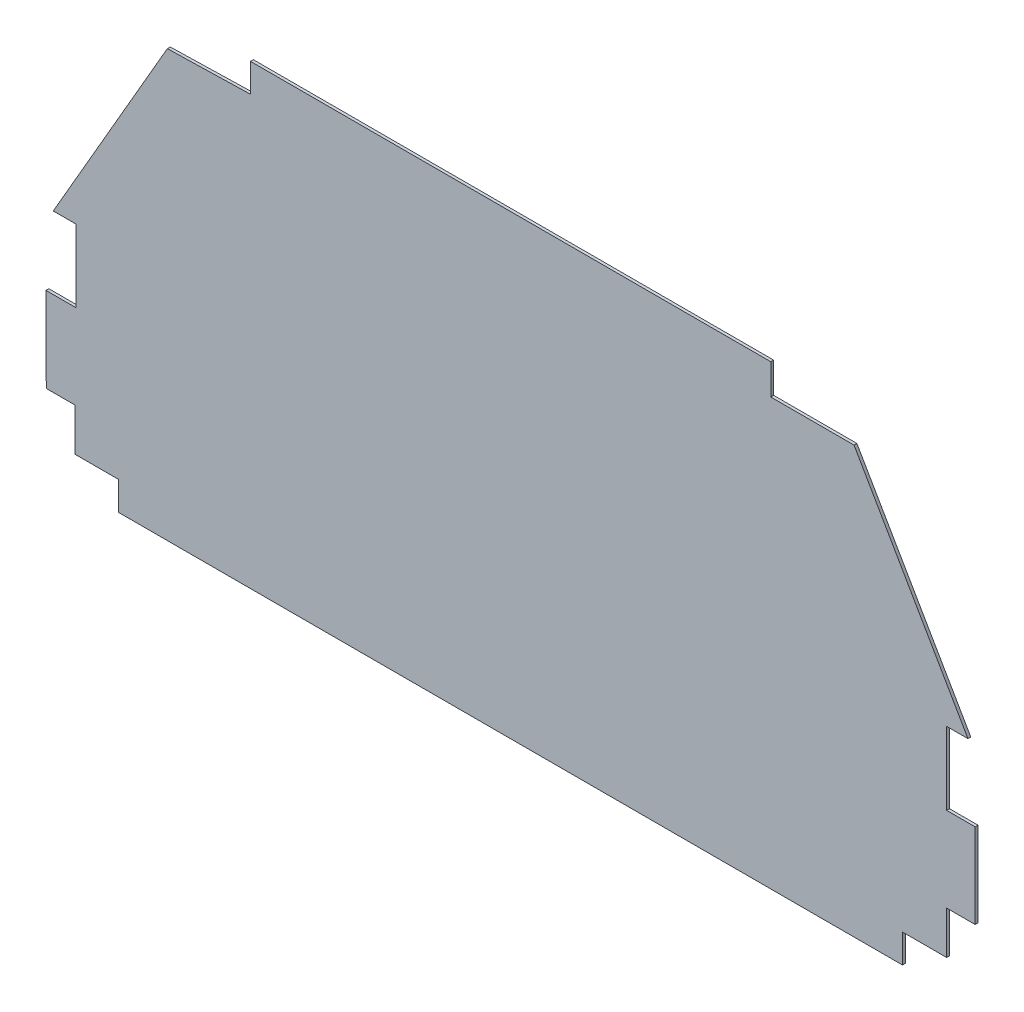
SolidWorks part; units mm, degrees
ref_plane "Front Plane" through (0, 0, 0) normal (0, 0, 1) x (1, 0, 0)
ref_plane "Top Plane" through (0, 0, 0) normal (0, 1, 0) x (1, 0, 0)
ref_plane "Right Plane" through (0, 0, 0) normal (1, 0, 0) x (0, 0, -1)
sketch "Sketch1" plane through (0, 0, 0) normal (0, 0, 1) x (1, 0, 0)
  line L24 (620.5018, 140.3021) -> (635.4651, 140.3021)
  line L25 (620.5018, 89.3201) -> (620.5018, 140.3021)
  line L26 (640.5004, 89.3201) -> (620.5018, 89.3201)
  line L27 (640.5004, 30.0075) -> (640.5004, 89.3201)
  line L28 (620.5018, 30.0075) -> (640.5004, 30.0075)
  line L29 (620.5018, -0.0004) -> (620.5018, 30.0075)
  line L30 (589.5897, -0.0004) -> (620.5018, -0.0004)
  line L31 (589.5897, -20.0284) -> (589.5897, -0.0004)
  line L32 (40.2838, -20.0284) -> (589.5897, -20.0284)
  line L33 (40.2838, -0.0004) -> (40.2838, -20.0284)
  line L34 (9.4987, -0.0004) -> (40.2838, -0.0004)
  line L35 (9.4987, 29.8802) -> (9.4987, -0.0004)
  line L36 (-10.5, 29.8802) -> (9.4987, 29.8802)
  line L37 (-10.6893, 89.3201) -> (-10.5, 29.8802)
  line L38 (10.2678, 89.3201) -> (-10.6893, 89.3201)
  line L39 (10.2678, 140.0532) -> (10.2678, 89.3201)
  line L40 (-5.6084, 140.0532) -> (10.2678, 140.0532)
  line L41 (74.3732, 278.5853) -> (-5.6084, 140.0532)
  line L42 (132.6371, 280.0026) -> (74.3732, 278.5853)
  line L43 (132.6371, 300.0013) -> (132.6371, 280.0026)
  line L44 (497.2893, 300.0013) -> (132.6371, 300.0013)
  line L45 (497.2893, 278.5853) -> (497.2893, 300.0013)
  line L46 (555.6273, 278.5853) -> (497.2893, 278.5853)
  line L47 (635.4651, 140.3021) -> (555.6273, 278.5853)
extrude "Boss-Extrude1" add sketch "Sketch1" along normal blind 2 contours L44 L43 L42 L41 L40 L39 L38 L37 L36 L35 L34 L33 L32 L31 L30 L29 L28 L27 L26 L25 L24 L47 L46 L45
